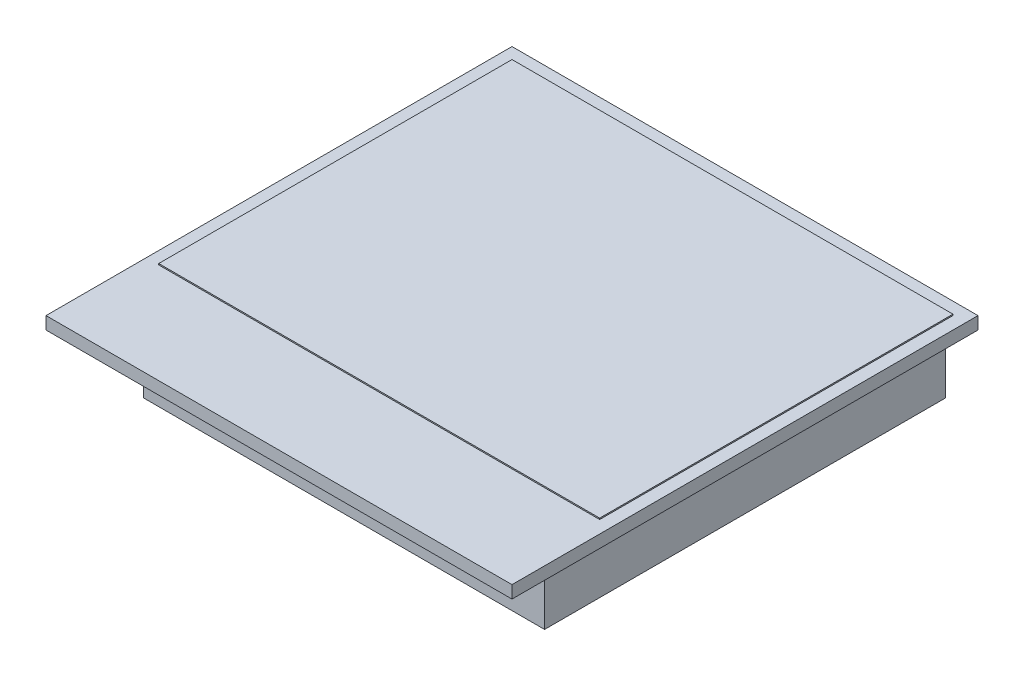
SolidWorks part; units mm, degrees
ref_plane "Front Plane" through (0, 0, 0) normal (0, 0, 1) x (1, 0, 0)
ref_plane "Top Plane" through (0, 0, 0) normal (0, 1, 0) x (1, 0, 0)
ref_plane "Right Plane" through (0, 0, 0) normal (1, 0, 0) x (0, 0, -1)
sketch "Sketch1" plane through (0, 0, 0) normal (0, 1, 0) x (1, 0, 0)
  line L1 (-9.3, 0) -> (9.3, 0)
  line L2 (-9.3, 0) -> (-9.3, 18.6)
  line L3 (-9.3, 18.6) -> (9.3, 18.6)
  line L4 (9.3, 0) -> (9.3, 18.6)
  point P4 (0, 0)
  dimension "D1" = 18.6
  dimension "D2" = 18.6
extrude "glass" add sketch "Sketch1" along normal blind 0.5
sketch "Sketch2" plane through (0, 0.5, 0) normal (0, 1, 0) x (1, 0, 0)
  line L0 (0, 4) -> (0, 0) construction
  line L1 (-8.8, 18.1) -> (8.8, 18.1)
  line L2 (-8.8, 18.1) -> (-8.8, 4)
  line L3 (-8.8, 4) -> (8.8, 4)
  line L4 (8.8, 18.1) -> (8.8, 4)
  line L5 (-9.3, 0) -> (9.3, 0) construction
  line L6 (-9.3, 18.6) -> (-9.3, 0) construction
  line L7 (9.3, 18.6) -> (-9.3, 18.6) construction
  dimension "D1" = 4
  dimension "D2" = 0.5
  dimension "D3" = 0.5
extrude "display" add sketch "Sketch2" along normal blind 0.05 separate body
sketch "Sketch3" plane through (0, 0, 0) normal (0, -1, 0) x (1, 0, 0)
  line L0 (0, 0) -> (0, -2.6) construction
  line L1 (-8, -2.6) -> (8, -2.6)
  line L2 (-8, -2.6) -> (-8, -18.6)
  line L3 (-8, -18.6) -> (8, -18.6)
  line L4 (8, -2.6) -> (8, -18.6)
  line L5 (-9.3, 0) -> (9.3, 0) construction
  line L6 (9.3, -18.6) -> (-9.3, -18.6) construction
  dimension "D1" = 16
  dimension "D2" = 16
extrude "sticky_foam" add sketch "Sketch3" along normal blind 3 separate body
sketch "Sketch4" plane through (0, 0, 0) normal (1, 0, 0) x (0, 0, -1)
  line L0 (0, 0) -> (0, -1) construction
  line L1 (0, -1) -> (-4, -1) construction
  circle A0 centre (-4, -1) radius 1.1642 construction
  dimension "D1" = 4
  dimension "D2" = 1
